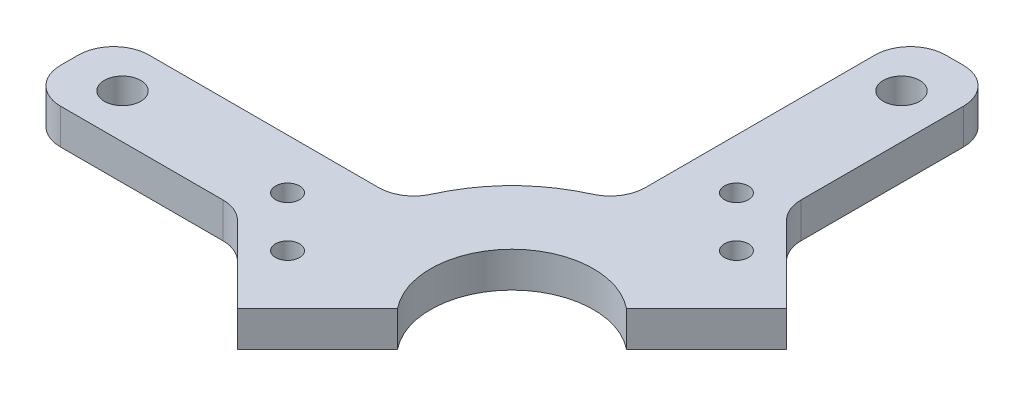
SolidWorks part; units mm, degrees
material "6061-T6 (SS)"
ref_plane "Front Plane" through (0, 0, 0) normal (0, 0, 1) x (1, 0, 0)
ref_plane "Top Plane" through (0, 0, 0) normal (0, 1, 0) x (1, 0, 0)
ref_plane "Right Plane" through (0, 0, 0) normal (1, 0, 0) x (0, 0, -1)
sketch "Sketch1" plane through (0, 0, 0) normal (0, 1, 0) x (1, 0, 0)
  circle A0 centre (0, 0) radius 14.605
  circle A1 centre (0, 0) radius 28.575
  dimension "D1" = 29.21
  dimension "D2" = 57.15
extrude "Boss-Extrude1" add sketch "Sketch1" along normal blind 6.35
sketch "Sketch2" plane through (0, 6.35, 0) normal (0, 1, 0) x (1, 0, 0)
  line L0 (73.025, -7.9375) -> (25.4, -7.9375)
  line L1 (79.375, -1.5875) -> (79.375, 1.5875)
  line L2 (25.4, -7.9375) -> (25.4, 7.9375)
  line L3 (73.025, 7.9375) -> (25.4, 7.9375)
  line L4 (79.375, -7.9375) -> (25.4, 7.9375) construction
  line L5 (25.4, -7.9375) -> (79.375, 7.9375) construction
  line L6 (0, -3.4925) -> (0, 3.4925) construction
  line L7 (52.3875, 0) -> (0, 0) construction
  arc A0 (79.375, -1.5875) -> (73.025, -7.9375) centre (73.025, -1.5875) cw
  arc A1 (79.375, 1.5875) -> (73.025, 7.9375) centre (73.025, 1.5875) ccw
  point P1 (52.3875, 0)
  dimension "D4" = 6.35
  dimension "D1" = 53.975
  dimension "D2" = 25.4
  dimension "D3" = 15.875
extrude "Boss-Extrude2" add sketch "Sketch2" against normal blind 6.35
hole_wizard "F (0.257) Diameter Hole1" positions "Sketch3" profile "Sketch4" hole size "F" standard "ANSI Inch" end condition through all
sketch "Sketch3" plane through (0, 6.35, 0) normal (0, 1, 0) x (1, 0, 0)
  line L0 (0, 0) -> (69.85, 0) construction
  point P0 (69.85, 0)
  point P9 (-69.85, 0)
  dimension "D1" = 69.85
sketch "Sketch4" plane through (69.85, 6.35, 0) normal (1, 0, 0) x (0, 0, 1)
  line L0 (0, 0) -> (0, 6.35)
  line L1 (0, 6.35) -> (3.2639, 6.35)
  line L2 (3.2639, 6.35) -> (3.2639, 0)
  line L5 (3.2639, 0) -> (0, 0)
  line L11 (0, -6.35) -> (0, 107.95) construction
  dimension "Thru Hole Dia." = 6.5278
  dimension "Thru Hole Depth" = 6.35
pattern_circular "CirPattern1" count 4 over 360 about axis through (0, 0, 0) along (0, 1, 0) of "Boss-Extrude2", "F (0.257) Diameter Hole1"
sketch "Sketch5" plane through (0, 6.35, 0) normal (0, 1, 0) x (1, 0, 0)
  line L0 (-38.2942, -36.0491) -> (36.0491, 38.2942)
  line L1 (-38.2942, -36.0491) -> (-36.0491, -38.2942)
  line L2 (36.0491, 38.2942) -> (38.2942, 36.0491)
  line L3 (-36.0491, -38.2942) -> (38.2942, 36.0491)
  line L4 (-38.2942, -36.0491) -> (38.2942, 36.0491) construction
  line L5 (36.0491, 38.2942) -> (-36.0491, -38.2942) construction
  line L6 (-3.4925, 0) -> (3.4925, 0) construction
  point P1 (0, 0)
  dimension "D1" = 45
  dimension "D2" = 3.175
extrude "Cut-Extrude1" cut sketch "Sketch5" against normal through all
fillet "Fillet1" radius 6.35 2 edges at (-7.9375, 3.175, -27.4504) (-27.4504, 3.175, -7.9375)
sketch "Sketch7" plane through (0, 6.35, 0) normal (0, 1, 0) x (1, 0, 0)
  line L0 (-14.5131, -12.2681) -> (-25.7385, -23.4934)
  line L1 (-14.5131, -12.2681) -> (-34.7187, 7.9375)
  line L2 (-25.7385, -23.4934) -> (-45.944, -3.2878)
  line L3 (-34.7187, 7.9375) -> (-45.944, -3.2878)
  line L4 (-11.3886, -9.1436) -> (-21.2969, -19.0518) construction
  line L6 (-31.8688, 7.9375) -> (-73.025, 7.9375) construction
  dimension "D1" = 28.575
  dimension "D2" = 15.875
extrude "Boss-Extrude3" add sketch "Sketch7" against normal blind 6.35
hole_wizard "#18 (0.1695) Diameter Hole1" positions "Sketch8" profile "Sketch9" hole size "#18" standard "ANSI Inch" end condition through all
sketch "Sketch8" plane through (0, 6.35, 0) normal (0, 1, 0) x (1, 0, 0)
  line L0 (-11.3886, -9.1436) -> (-25.7385, -23.4934) construction
  line L1 (-21.2483, -19.0033) -> (-39.2088, -1.0428) construction
  line L3 (-41.2944, -7.9375) -> (-25.7385, -23.4934) construction
  point P0 (-30.2286, -10.023)
  point P2 (-39.2088, -1.0428)
  point P9 (-24.8627, -15.1581)
  point P10 (-33.8929, -6.1279)
  point P11 (-33.8725, -6.1075)
  dimension "D1" = 25.4
  dimension "D2" = 12.7
  dimension "D3" = 6.35
sketch "Sketch9" plane through (-30.2286, 6.35, 10.023) normal (1, 0, 0) x (0, 0, 1)
  line L0 (0, 0) -> (0, 6.35)
  line L1 (0, 6.35) -> (2.1526, 6.35)
  line L2 (2.1526, 6.35) -> (2.1526, 0)
  line L5 (2.1526, 0) -> (0, 0)
  line L11 (0, -6.35) -> (0, 107.95) construction
  dimension "Thru Hole Dia." = 4.3053
  dimension "Thru Hole Depth" = 6.35
ref_plane "Plane2" through (0, 0, 0) normal (0.7071, 0, -0.7071) x (-0.7071, 0, -0.7071)
mirror "Mirror1" about plane through (0, 0, 0) normal (0.7071, 0, -0.7071) of "#18 (0.1695) Diameter Hole1", "Boss-Extrude3"
fillet "Fillet2" radius 6.35 2 edges at (7.9375, 3.175, -41.2944) (-41.2944, 3.175, 7.9375)
